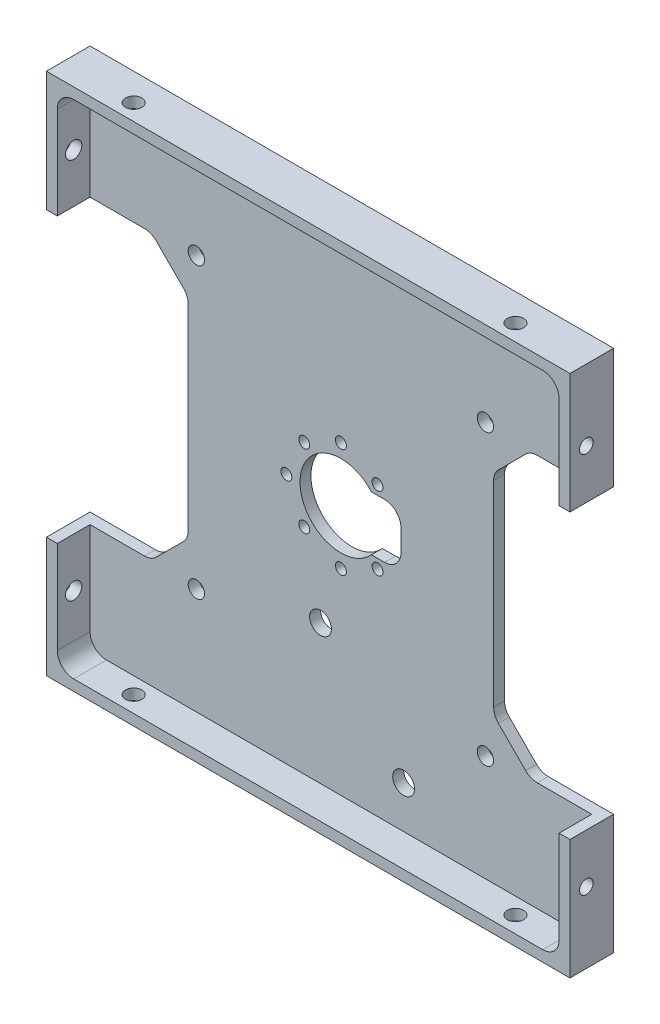
SolidWorks part; units mm, degrees
material "6061-T6 (SS)"
ref_plane "Front" through (0, 0, 0) normal (0, 0, 1) x (1, 0, 0)
ref_plane "Top" through (0, 0, 0) normal (0, 1, 0) x (1, 0, 0)
ref_plane "Right" through (0, 0, 0) normal (1, 0, 0) x (0, 0, -1)
sketch "Sketch1" plane through (0, 0, 0) normal (0, 0, 1) x (1, 0, 0)
  line L1 (-48, -48) -> (48, -48)
  line L2 (-48, -48) -> (-48, 48)
  line L3 (-48, 48) -> (48, 48)
  line L4 (48, -48) -> (48, 48)
  line L5 (-48, -48) -> (48, 48) construction
  line L6 (-48, 48) -> (48, -48) construction
  point P0 (0, 0)
  dimension "D1" = 96
  dimension "D2" = 96
extrude "Boss-Extrude1" add sketch "Sketch1" along normal blind 8
sketch "Sketch2" plane through (0, 0, 8) normal (0, 0, 1) x (1, 0, 0)
  line L1 (46, -46) -> (-46, -46)
  line L2 (46, -46) -> (46, 46)
  line L3 (46, 46) -> (-46, 46)
  line L4 (-46, -46) -> (-46, 46)
  line L5 (46, -46) -> (-46, 46) construction
  line L6 (46, 46) -> (-46, -46) construction
  point P0 (0, 0)
  dimension "D1" = 92
  dimension "D2" = 92
extrude "Component Platform" cut sketch "Sketch2" against normal blind 6
sketch "Sketch3" plane through (0, 0, 2) normal (0, 0, 1) x (1, 0, 0)
  line L1 (-33.8787, -25.1213) -> (-28.8787, -20.1213)
  line L2 (-33.8787, 25.1213) -> (-28.8787, 20.1213)
  line L3 (-28, -18) -> (-28, 18)
  line L4 (-48, -26) -> (-36, -26)
  line L7 (-48, 48) -> (-48, -48) construction
  line L8 (0, -56.7987) -> (0, 73.4321) construction
  line L9 (46, -46) -> (-57.8147, 57.8147) construction
  line L18 (46, 46) -> (-68.5705, -68.5705) construction
  line L23 (-48, 26) -> (-36, 26)
  line L26 (-48, -26) -> (-48, 26)
  line L28 (-48, -48) -> (48, -48) construction
  line L29 (48, -26) -> (48, 26)
  line L30 (48, 26) -> (36, 26)
  line L31 (33.8787, 25.1213) -> (28.8787, 20.1213)
  line L32 (28, -18) -> (28, 18)
  line L33 (33.8787, -25.1213) -> (28.8787, -20.1213)
  line L34 (48, -26) -> (36, -26)
  arc A3 (-28.8787, -20.1213) -> (-28, -18) centre (-31, -18) ccw
  arc A4 (-28.8787, 20.1213) -> (-28, 18) centre (-31, 18) cw
  arc A13 (-33.8787, -25.1213) -> (-36, -26) centre (-36, -23) cw
  arc A15 (-33.8787, 25.1213) -> (-36, 26) centre (-36, 23) ccw
  arc A17 (33.8787, 25.1213) -> (36, 26) centre (36, 23) cw
  arc A18 (28.8787, 20.1213) -> (28, 18) centre (31, 18) ccw
  arc A19 (28.8787, -20.1213) -> (28, -18) centre (31, -18) cw
  arc A20 (33.8787, -25.1213) -> (36, -26) centre (36, -23) ccw
  point P0 (-48, 0)
  point P37 (-48, 0)
  dimension "D2" = 3
  dimension "D3" = 3
  dimension "D4" = 20
  dimension "D6" = 3
  dimension "D7" = 3
  dimension "D8" = 135
  dimension "D5" = 52
  dimension "D9" = 135
  dimension "D10" = 12
  dimension "D11" = 12
  dimension "D12" = 48
extrude "Cable Slots" cut sketch "Sketch3" against normal mid plane 12
sketch "Sketch4" plane through (0, 0, 2) normal (0, 0, 1) x (1, 0, 0)
  circle A0 centre (0, 0) radius 7.5
  dimension "D1" = 15
extrude "Center Mass Cut" cut sketch "Sketch4" against normal blind 6
ref_plane "Center Y-Plane" through (0, 0, 0) normal (1, 0, 0) x (0, 0, -1)
ref_plane "Center X-Plane" through (0, 0, 0) normal (0, -1, 0) x (-1, 0, 0)
fillet "Inner Corner Fillets" radius 3 4 edges at (46, -46, 5) (-46, -46, 5) (46, 46, 5) (-46, 46, 5)
sketch "Sketch10" plane through (0, 0, 2) normal (0, 0, 1) x (1, 0, 0)
  line L1 (0, -5) -> (11, -5)
  line L2 (11, -5) -> (11, 5)
  line L3 (11, 5) -> (0, 5)
  line L5 (0, -5) -> (0, 5)
  point P3 (0, 0)
  dimension "D1" = 10
  dimension "D3" = 11
extrude "Motor Cutout" cut sketch "Sketch10" against normal blind 2
fillet "Fillet1" radius 3 2 edges at (11, 5, 1) (11, -5, 1)
sketch "Sketch11" plane through (0, 0, 2) normal (0, 0, 1) x (1, 0, 0)
  line L0 (0, 0) -> (0, 23.9217) construction
  line L1 (0, 0) -> (0, -24.7081) construction
  line L2 (0, 0) -> (-16.3847, 0) construction
  line L3 (0, 0) -> (16.7779, 0) construction
  circle A0 centre (6.72, 6.72) radius 1.05
  circle A1 centre (-6.72, 6.72) radius 1.05
  circle A2 centre (-6.72, -6.72) radius 1.05
  circle A3 centre (6.72, -6.72) radius 1.05
  circle A4 centre (0, 10) radius 1.05
  circle A5 centre (-10, 0) radius 1.05
  circle A6 centre (0, -10) radius 1.05
  dimension "D9" = 2.1
  dimension "D1" = 6.72
  dimension "D2" = 6.72
  dimension "D3" = 6.72
  dimension "D4" = 6.72
  dimension "D5" = 6.72
  dimension "D6" = 6.72
  dimension "D7" = 6.72
  dimension "D8" = 6.72
  dimension "D10" = 10
  dimension "D11" = 10
  dimension "D12" = 10
sketch "Sketch12" plane through (48, 0, 0) normal (1, 0, 0) x (0, 0, -1)
  line L0 (-5, -48) -> (-5, 48) construction
  line L1 (-8, -48) -> (0, -48) construction
  line L2 (-8, 48) -> (0, 48) construction
  line L3 (-8, -48) -> (-8, -26) construction
  dimension "D1" = 3
hole_wizard "M3x0.5 Tapped Hole1" positions "Sketch13" profile "Sketch14" tap size "M3x0.5" standard "ANSI Metric" end condition up to next
sketch "Sketch13" plane through (48, 0, 0) normal (1, 0, 0) x (0, 0, -1)
  line L0 (-5, -48) -> (-5, 48) construction
  point P0 (-5, -35)
  point P4 (-5, 35)
  dimension "D1" = 70
  dimension "D2" = 35
sketch "Sketch14" plane through (48, -35, 5) normal (0, 1, 0) x (0, 0, -1)
  line L0 (0, 0) -> (0, 2)
  line L1 (0, 2) -> (1.25, 2)
  line L2 (1.25, 2) -> (1.25, 0)
  line L5 (1.25, 0) -> (0, 0)
  line L11 (0, -6.35) -> (0, 107.95) construction
  dimension "Thread Major Dia." = 2.5
  dimension "Thru Tap Drill Depth" = 2
sketch "Sketch15" plane through (0, 48, 0) normal (0, 1, 0) x (1, 0, 0)
  line L0 (-48, -5) -> (48, -5) construction
  line L1 (-48, -8) -> (-48, 0) construction
  line L2 (48, -8) -> (48, 0) construction
  line L3 (48, -8) -> (-48, -8) construction
  dimension "D1" = 3
hole_wizard "Ø3.0mm Dowel Hole1" positions "Sketch16" profile "Sketch17" hole size "Ø3.0" standard "ANSI Metric" end condition up to next
sketch "Sketch16" plane through (0, 48, 0) normal (0, 1, 0) x (1, 0, 0)
  line L0 (-48, -5) -> (48, -5) construction
  point P0 (35, -5)
  point P4 (-35, -5)
  dimension "D1" = 70
  dimension "D2" = 35
sketch "Sketch17" plane through (35, 48, 5) normal (1, 0, 0) x (0, 0, 1)
  line L0 (0, 0) -> (0, 2)
  line L1 (0, 2) -> (1.5, 2)
  line L2 (1.5, 2) -> (1.5, 0)
  line L5 (1.5, 0) -> (0, 0)
  line L11 (0, -6.35) -> (0, 107.95) construction
  dimension "Thru Hole Dia." = 3
  dimension "Thru Hole Depth" = 2
mirror "Mirror2" about plane through (0, 0, 0) normal (0, -1, 0) of "Ø3.0mm Dowel Hole1"
sketch "Sketch18" plane through (0, 0, 2) normal (0, 0, 1) x (1, 0, 0)
  line L0 (0, -46) -> (0, 46) construction
  line L1 (-43, -46) -> (43, -46) construction
  line L2 (43, 46) -> (-43, 46) construction
  line L6 (46, -28.5) -> (-46, -28.5) construction
  line L7 (46, -43) -> (46, -26) construction
  line L8 (-46, -26) -> (-46, -43) construction
  line L9 (-28.5, -46) -> (-28.5, 46) construction
  line L10 (-43, -46) -> (43, -46) construction
  dimension "D1" = 17.5
  dimension "D2" = 28.5
hole_wizard "Ø3.0mm Dowel Hole2" positions "Sketch19" profile "Sketch20" hole size "Ø3.0" standard "ANSI Metric" end condition up to next
sketch "Sketch19" plane through (0, 0, 2) normal (0, 0, 1) x (1, 0, 0)
  line L20 (-43, -46) -> (43, -46) construction
  line L21 (-46, -26) -> (-46, -43) construction
  line L26 (43, 46) -> (-43, 46) construction
  line L27 (46, 26) -> (46, 43) construction
  line L28 (46, -43) -> (46, -26) construction
  line L29 (-46, 43) -> (-46, 26) construction
  point P49 (-26.5, -26.5)
  point P56 (-26.5, -26.5)
  point P67 (26.5, -26.5)
  point P70 (26.5, 26.5)
  point P73 (-26.5, 26.5)
  point P83 (26.5, -26.5)
  point P85 (26.5, 26.5)
  point P87 (-26.5, 26.5)
  dimension "D1" = 19.5
  dimension "D2" = 19.5
  dimension "D3" = 19.5
  dimension "D4" = 19.5
  dimension "D5" = 19.5
  dimension "D6" = 19.5
  dimension "D7" = 19.5
  dimension "D8" = 19.5
sketch "Sketch20" plane through (-26.5, -26.5, 2) normal (1, 0, 0) x (0, -1, 0)
  line L0 (0, 0) -> (0, 2)
  line L1 (0, 2) -> (1.5, 2)
  line L2 (1.5, 2) -> (1.5, 0)
  line L5 (1.5, 0) -> (0, 0)
  line L11 (0, -6.35) -> (0, 107.95) construction
  dimension "Thru Hole Dia." = 3
  dimension "Thru Hole Depth" = 2
hole_wizard "Ø2.0mm Dowel Hole1" positions "Sketch23" profile "Sketch24" hole size "Ø2.0" standard "ANSI Metric" end condition up to next
sketch "Sketch23" plane through (0, 0, 2) normal (0, 0, 1) x (1, 0, 0)
  point P0 (6.72, -6.72)
  point P3 (0, -10)
  point P6 (-6.72, -6.72)
  point P9 (-10, 0)
  point P12 (-6.72, 6.72)
  point P15 (0, 10)
  point P18 (6.72, 6.72)
sketch "Sketch24" plane through (6.72, -6.72, 2) normal (1, 0, 0) x (0, -1, 0)
  line L0 (0, 0) -> (0, 2)
  line L1 (0, 2) -> (1, 2)
  line L2 (1, 2) -> (1, 0)
  line L5 (1, 0) -> (0, 0)
  line L11 (0, -6.35) -> (0, 107.95) construction
  dimension "Thru Hole Dia." = 2
  dimension "Thru Hole Depth" = 2
sketch "Sketch25" plane through (0, 0, 2) normal (0, 0, 1) x (1, 0, 0)
  line L0 (0, -46) -> (0, 46) construction
  line L1 (-43, -46) -> (43, -46) construction
  line L2 (43, 46) -> (-43, 46) construction
  line L3 (-46, -38.25) -> (46, -38.25) construction
  line L4 (-46, -26) -> (-46, -43) construction
  line L5 (46, -43) -> (46, -26) construction
  line L6 (-43, -46) -> (43, -46) construction
  point P14 (11.5, -38.25)
  point P15 (-3.74, -20.47)
  dimension "D1" = 7.75
  dimension "D2" = 11.5
  dimension "D3" = 15.24
  dimension "D4" = 17.78
hole_wizard "Ø4.0mm Dowel Hole1" positions "Sketch26" profile "Sketch27" hole size "Ø4.0" standard "ANSI Metric" end condition up to next
sketch "Sketch26" plane through (0, 0, 2) normal (0, 0, 1) x (1, 0, 0)
  point P0 (-3.74, -20.47)
  point P3 (11.5, -38.25)
sketch "Sketch27" plane through (-3.74, -20.47, 2) normal (1, 0, 0) x (0, -1, 0)
  line L0 (0, 0) -> (0, 2)
  line L1 (0, 2) -> (2, 2)
  line L2 (2, 2) -> (2, 0)
  line L5 (2, 0) -> (0, 0)
  line L11 (0, -6.35) -> (0, 107.95) construction
  dimension "Thru Hole Dia." = 4
  dimension "Thru Hole Depth" = 2
sketch "Sketch28" plane through (-48, 0, 0) normal (-1, 0, 0) x (0, 0, 1)
  line L0 (8, 48) -> (8, 26) construction
  line L1 (8, 48) -> (0, 48) construction
  line L2 (5, 48) -> (5, 26) construction
  line L3 (0, 26) -> (8, 26) construction
  point P12 (5, 35)
  dimension "D1" = 13
  dimension "D2" = 3
sketch "Sketch29" plane through (-48, 0, 0) normal (-1, 0, 0) x (0, 0, 1)
  line L0 (8, -26) -> (8, -48) construction
  line L3 (8, -48) -> (0, -48) construction
  line L5 (5, -48) -> (5, -26) construction
  line L6 (0, -26) -> (8, -26) construction
  point P10 (5, -35)
  dimension "D1" = 3
  dimension "D2" = 13
hole_wizard "Ø3.0mm Dowel Hole3" positions "3DSketch1" profile "Sketch30" hole size "Ø3.0" standard "ANSI Metric" end condition up to next
sketch3d "3DSketch1"
  point P0 (-48, 35, 5)
  point P3 (-48, -35, 5)
sketch "Sketch30" plane through (-48, 35, 5) normal (0, 1, 0) x (0, 0, 1)
  line L0 (0, 0) -> (0, 2)
  line L1 (0, 2) -> (1.5, 2)
  line L2 (1.5, 2) -> (1.5, 0)
  line L5 (1.5, 0) -> (0, 0)
  line L11 (0, -6.35) -> (0, 107.95) construction
  dimension "Thru Hole Dia." = 3
  dimension "Thru Hole Depth" = 2
